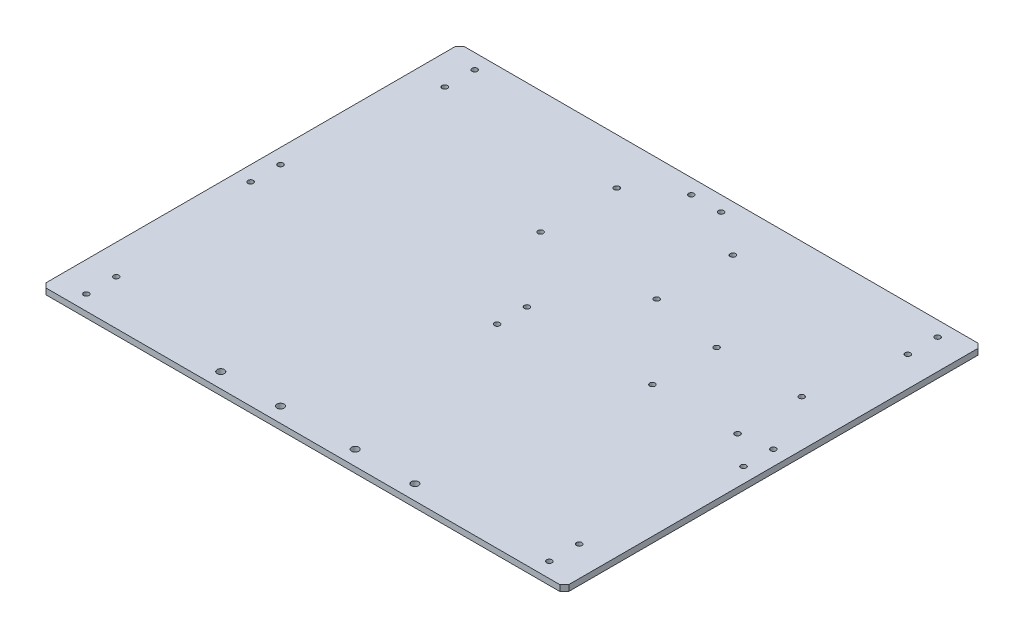
SolidWorks part; units mm, degrees
material "ABS PC"
ref_plane "Ebene vorne" through (0, 0, 0) normal (0, 0, 1) x (1, 0, 0)
ref_plane "Ebene oben" through (0, 0, 0) normal (0, 1, 0) x (1, 0, 0)
ref_plane "Ebene rechts" through (0, 0, 0) normal (1, 0, 0) x (0, 0, -1)
sketch "Skizze1" plane through (0, 0, 0) normal (0, 1, 0) x (1, 0, 0)
  line L1 (-175, 140) -> (175, 140)
  line L2 (-175, 140) -> (-175, -140)
  line L3 (-175, -140) -> (175, -140)
  line L4 (175, 140) -> (175, -140)
  circle A3 centre (-38.875, 109) radius 1.8
  circle A4 centre (-38.875, 58) radius 1.8
  circle A5 centre (38.875, 109) radius 1.8
  circle A6 centre (38.875, 58) radius 1.8
  circle A7 centre (87, 50) radius 1.8
  circle A8 centre (87, 7) radius 1.8
  circle A9 centre (144, 7) radius 1.8
  circle A10 centre (144, 50) radius 1.8
  point P4 (0, 140)
  point P6 (175, 0)
  point P7 (0, 0)
  dimension "D3" = 190
  dimension "D4" = 249
  dimension "D1" = 280
  dimension "D2" = 350
  dimension "D5" = 38.875
  dimension "D6" = 51
  dimension "D7" = 77.75
  dimension "D8" = 87
  dimension "D9" = 43
  dimension "D10" = 57
extrude "Aufsatz-Linear austragen1" add sketch "Skizze1" along normal blind 4
chamfer "Fase1" distance 3 angle 45 4 edges at (175, 2, 140) (175, 2, -140) (-175, 2, 140) (-175, 2, -140)
hole_wizard "Durchgangsloch für M31" positions "Skizze2" profile "Skizze3" hole size "M3" standard "DIN" end condition through all
sketch "Skizze2" plane through (0, 4, 0) normal (0, 1, 0) x (1, 0, 0)
  line L0 (-175, 137) -> (-175, -137) construction
  line L1 (172, 140) -> (-172, 140) construction
  point P0 (-155, 130)
  point P2 (-155, 110)
  point P9 (0, 0)
  dimension "D1" = 20
  dimension "D2" = 10
  dimension "D3" = 20
sketch "Skizze3" plane through (-155, 4, -130) normal (1, 0, 0) x (0, 0, 1)
  line L0 (0, 0) -> (0, 4)
  line L1 (0, 4) -> (1.8, 4)
  line L2 (1.8, 4) -> (1.8, 0)
  line L5 (1.8, 0) -> (0, 0)
  line L11 (0, -6.35) -> (0, 107.95) construction
  dimension "Bohrerdurchmesser" = 3.6
  dimension "Bohrungstiefe" = 4
mirror "Spiegeln1" about plane through (0, 0, 0) normal (1, 0, 0) of "Durchgangsloch für M31"
mirror "Spiegeln2" about plane through (0, 0, 0) normal (0, 0, 1) of "Durchgangsloch für M31", "Spiegeln1"
hole_wizard "Durchgangsloch für M32" positions "Skizze4" profile "Skizze5" hole size "M3" standard "DIN" end condition through all
sketch "Skizze4" plane through (0, 4, 0) normal (0, 1, 0) x (1, 0, 0)
  line L0 (0, -55) -> (0, 55) construction
  point P0 (0, 10)
  point P4 (0, -10)
  point P14 (0, 0)
  point P15 (0, 0)
  dimension "D1" = 10
  dimension "D2" = 10
sketch "Skizze5" plane through (0, 4, -10) normal (1, 0, 0) x (0, 0, 1)
  line L0 (0, 0) -> (0, 4)
  line L1 (0, 4) -> (1.8, 4)
  line L2 (1.8, 4) -> (1.8, 0)
  line L5 (1.8, 0) -> (0, 0)
  line L11 (0, -6.35) -> (0, 107.95) construction
  dimension "Bohrerdurchmesser" = 3.6
  dimension "Bohrungstiefe" = 4
hole_wizard "Durchgangsloch für M42" positions "Skizze8" profile "Skizze9" hole size "M4" standard "DIN" end condition through all
sketch "Skizze8" plane through (0, 4, 0) normal (0, 1, 0) x (1, 0, 0)
  line L0 (-172, -140) -> (172, -140) construction
  point P0 (-65, -130)
  point P2 (-25, -130)
  point P4 (25, -130)
  point P6 (65, -130)
  point P15 (0, 0)
  dimension "D1" = 40
  dimension "D2" = 40
  dimension "D3" = 10
  dimension "D4" = 50
  dimension "D5" = 25
sketch "Skizze9" plane through (-65, 4, 130) normal (1, 0, 0) x (0, 0, 1)
  line L0 (0, 0) -> (0, 4)
  line L1 (0, 4) -> (2.4, 4)
  line L2 (2.4, 4) -> (2.4, 0)
  line L5 (2.4, 0) -> (0, 0)
  line L11 (0, -6.35) -> (0, 107.95) construction
  dimension "Bohrerdurchmesser" = 4.8
  dimension "Bohrungstiefe" = 4
hole_wizard "Durchgangsloch für M34" positions "Skizze10" profile "Skizze11" hole size "M3" standard "DIN" end condition through all
sketch "Skizze10" plane through (0, 4, 0) normal (0, 1, 0) x (1, 0, 0)
  line L0 (-175, 137) -> (-175, -137) construction
  line L1 (172, 140) -> (-172, 140) construction
  point P0 (-165, 10)
  point P2 (-165, -10)
  point P9 (-10, 130)
  dimension "D1" = 20
  dimension "D2" = 10
  dimension "D3" = 10
  dimension "D4" = 10
  dimension "D5" = 10
sketch "Skizze11" plane through (-165, 4, -10) normal (1, 0, 0) x (0, 0, 1)
  line L0 (0, 0) -> (0, 4)
  line L1 (0, 4) -> (1.8, 4)
  line L2 (1.8, 4) -> (1.8, 0)
  line L5 (1.8, 0) -> (0, 0)
  line L11 (0, -6.35) -> (0, 107.95) construction
  dimension "Bohrerdurchmesser" = 3.6
  dimension "Bohrungstiefe" = 4
mirror "Spiegeln3" about plane through (0, 0, 0) normal (1, 0, 0) of "Durchgangsloch für M34"
